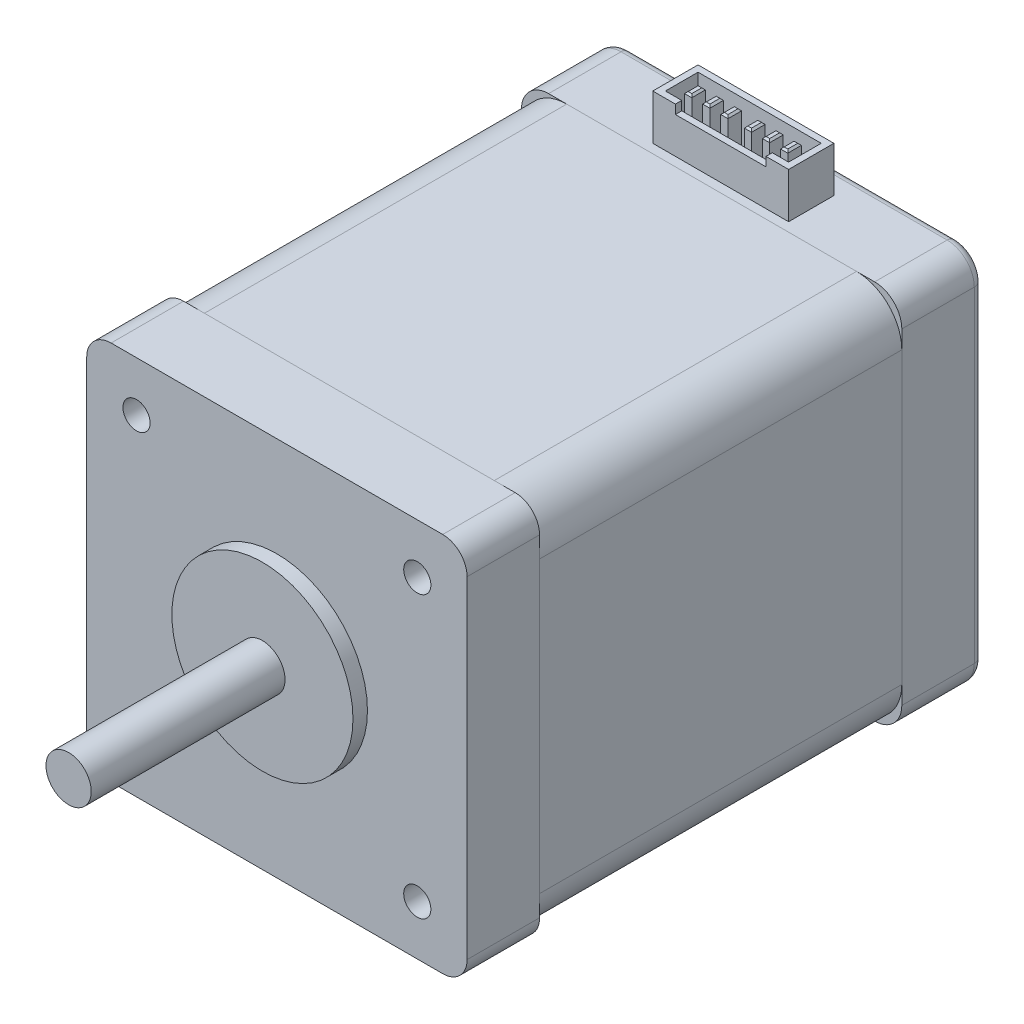
SolidWorks part; units mm, degrees
ref_plane "Front Plane" through (0, 0, 0) normal (0, 0, 1) x (1, 0, 0)
ref_plane "Top Plane" through (0, 0, 0) normal (0, 1, 0) x (1, 0, 0)
ref_plane "Right Plane" through (0, 0, 0) normal (1, 0, 0) x (0, 0, -1)
sketch "Sketch1" plane through (0, 0, 0) normal (0, 0, 1) x (1, 0, 0)
  line L0 (0, -25.0824) -> (0, 25.0824) construction
  line L1 (27.865, 0) -> (-27.865, 0) construction
  line L2 (-18.3073, -21) -> (18.3073, -21)
  line L3 (-21, -18.3073) -> (-21, 18.3073)
  line L4 (-18.3073, 21) -> (18.3073, 21)
  line L5 (21, -18.3073) -> (21, 18.3073)
  line L6 (-21, -21) -> (21, 21) construction
  line L7 (-21, 21) -> (21, -21) construction
  line L8 (-15.5, 15.5) -> (-15.5, -15.5) construction
  line L9 (-15.5, -15.5) -> (15.5, -15.5) construction
  line L10 (15.5, -15.5) -> (15.5, 15.5) construction
  line L11 (15.5, 15.5) -> (-15.5, 15.5) construction
  circle A0 centre (-15.5, 15.5) radius 1.5
  circle A1 centre (15.5, 15.5) radius 1.5
  circle A2 centre (15.5, -15.5) radius 1.5
  circle A3 centre (-15.5, -15.5) radius 1.5
  arc A4 (-21, -18.3073) -> (-18.3073, -21) centre (-18.3073, -18.3073) ccw
  arc A5 (-18.3073, 21) -> (-21, 18.3073) centre (-18.3073, 18.3073) ccw
  arc A6 (21, 18.3073) -> (18.3073, 21) centre (18.3073, 18.3073) ccw
  arc A7 (18.3073, -21) -> (21, -18.3073) centre (18.3073, -18.3073) ccw
  point P0 (0, 0)
  point P4 (0, 0)
  point P13 (0, 0)
  point P35 (0, 0)
  dimension "D3" = 3
  dimension "D1" = 42
  dimension "D2" = 42
  dimension "D4" = 31
  dimension "D5" = 4
extrude "Boss-Extrude1" add sketch "Sketch1" along normal blind 8
sketch "Sketch2" plane through (0, 0, 8) normal (0, 0, 1) x (1, 0, 0)
  circle A0 centre (0, 0) radius 2.5
  dimension "D1" = 5
extrude "Boss-Extrude2" add sketch "Sketch2" along normal blind 23
sketch "Sketch3" plane through (0, 0, 0) normal (0, 0, -1) x (-1, 0, 0)
  line L1 (-21, -21) -> (21, -21)
  line L2 (-21, -21) -> (-21, 21)
  line L3 (-21, 21) -> (21, 21)
  line L4 (21, -21) -> (21, 21)
  line L5 (-21, -21) -> (21, 21) construction
  line L6 (-21, 21) -> (21, -21) construction
  point P0 (0, 0)
  dimension "D1" = 42
  dimension "D2" = 42
extrude "Boss-Extrude3" add sketch "Sketch3" along normal blind 40 separate body
sketch "Sketch4" plane through (0, 0, -40) normal (0, 0, -1) x (-1, 0, 0)
  line L0 (21, -21) -> (21, 21) construction
  line L1 (-21, -21) -> (21, -21) construction
  line L2 (-21, 21) -> (-21, -21) construction
  line L3 (21, 21) -> (-21, 21) construction
  line L4 (21, -21) -> (21, 21)
  line L5 (-21, -21) -> (21, -21)
  line L6 (-21, 21) -> (-21, -21)
  line L7 (21, 21) -> (-21, 21)
extrude "Boss-Extrude4" add sketch "Sketch4" along normal blind 9 separate body
fillet "Fillet1" radius 3 4 edges at (-21, -21, -44.5) (21, -21, -44.5) (21, 21, -44.5) (-21, 21, -44.5)
fillet "Fillet3" radius 5 4 edges at (-21, 21, -20) (-21, -21, -20) (21, -21, -20) (21, 21, -20)
sketch "Sketch5" plane through (0, 0, -49) normal (0, 0, -1) x (-1, 0, 0)
  circle A0 centre (-15.5, 15.5) radius 1.5 construction
  circle A1 centre (-15.5, 15.5) radius 1.5
  circle A2 centre (-15.5, -15.5) radius 1.5 construction
  circle A3 centre (-15.5, -15.5) radius 1.5
  circle A4 centre (15.5, 15.5) radius 1.5 construction
  circle A5 centre (15.5, 15.5) radius 1.5
  circle A6 centre (15.5, -15.5) radius 1.5 construction
  circle A7 centre (15.5, -15.5) radius 1.5
extrude "Cut-Extrude1" cut sketch "Sketch5" against normal through all
sketch "Sketch6" plane through (0, 0, 8) normal (0, 0, 1) x (1, 0, 0)
  circle A0 centre (0, 0) radius 10
  circle A1 centre (0, 0) radius 2.5 construction
  circle A2 centre (0, 0) radius 2.5
  dimension "D1" = 20
extrude "Boss-Extrude5" add sketch "Sketch6" along normal blind 1.6
sketch "Sketch7" plane through (0, 21, 0) normal (0, 1, 0) x (1, 0, 0)
  line L0 (0, 0) -> (0, 52.3283) construction
  line L1 (0, 46) -> (-7.5, 46)
  line L2 (-7.5, 46) -> (-7.5, 41)
  line L3 (-7.5, 41) -> (7.5, 41)
  line L4 (7.5, 41) -> (7.5, 46)
  line L5 (7.5, 46) -> (0, 46)
  line L6 (-18, 49) -> (18, 49) construction
  line L7 (0, 45.3) -> (-6.8, 45.3)
  line L8 (-6.8, 45.3) -> (-6.8, 41.7)
  line L9 (-6.8, 41.7) -> (0, 41.7)
  line L10 (0, 41.7) -> (6.8, 41.7)
  line L11 (6.8, 41.7) -> (6.8, 45.3)
  line L12 (6.8, 45.3) -> (0, 45.3)
  line L13 (-6.2801, 43.457) -> (-4.7801, 43.457) construction
  line L15 (-5.7, 42.707) -> (-4.9, 42.707)
  line L16 (-5.7, 42.707) -> (-5.7, 44.207)
  line L17 (-5.7, 44.207) -> (-4.9, 44.207)
  line L18 (-4.9, 42.707) -> (-4.9, 44.207)
  line L19 (-5.7, 42.707) -> (-4.9, 44.207) construction
  line L20 (-5.7, 44.207) -> (-4.9, 42.707) construction
  line L21 (-3.7, 42.707) -> (-2.9, 42.707)
  line L22 (-3.7, 42.707) -> (-3.7, 44.207)
  line L23 (-3.7, 44.207) -> (-2.9, 44.207)
  line L24 (-2.9, 42.707) -> (-2.9, 44.207)
  line L25 (-3.7, 42.707) -> (-2.9, 44.207) construction
  line L26 (-3.7, 44.207) -> (-2.9, 42.707) construction
  line L27 (-0.9, 42.707) -> (-1.7, 42.707)
  line L28 (-0.9, 42.707) -> (-0.9, 44.207)
  line L29 (-0.9, 44.207) -> (-1.7, 44.207)
  line L30 (-1.7, 42.707) -> (-1.7, 44.207)
  line L31 (-0.9, 42.707) -> (-1.7, 44.207) construction
  line L32 (-0.9, 44.207) -> (-1.7, 42.707) construction
  line L33 (0.9, 42.707) -> (1.7, 42.707)
  line L34 (0.9, 42.707) -> (0.9, 44.207)
  line L35 (0.9, 44.207) -> (1.7, 44.207)
  line L36 (1.7, 42.707) -> (1.7, 44.207)
  line L37 (0.9, 42.707) -> (1.7, 44.207) construction
  line L38 (0.9, 44.207) -> (1.7, 42.707) construction
  line L39 (2.9, 42.707) -> (3.7, 42.707)
  line L40 (2.9, 42.707) -> (2.9, 44.207)
  line L41 (2.9, 44.207) -> (3.7, 44.207)
  line L42 (3.7, 42.707) -> (3.7, 44.207)
  line L43 (2.9, 42.707) -> (3.7, 44.207) construction
  line L44 (2.9, 44.207) -> (3.7, 42.707) construction
  line L45 (4.9, 42.707) -> (5.7, 42.707)
  line L46 (4.9, 42.707) -> (4.9, 44.207)
  line L47 (4.9, 44.207) -> (5.7, 44.207)
  line L48 (5.7, 42.707) -> (5.7, 44.207)
  line L49 (4.9, 42.707) -> (5.7, 44.207) construction
  line L50 (4.9, 44.207) -> (5.7, 42.707) construction
  point P18 (-5.3, 43.457)
  point P23 (-3.3, 43.457)
  point P28 (-1.3, 43.457)
  point P33 (1.3, 43.457)
  point P38 (3.3, 43.457)
  point P43 (5.3, 43.457)
  dimension "D1" = 15
  dimension "D2" = 3
  dimension "D3" = 5
  dimension "D4" = 0.7
  dimension "D5" = 0.7
  dimension "D6" = 0.7
  dimension "D7" = 1.843
  dimension "D8" = 1.5
  dimension "D9" = 0.8
  dimension "D10" = 0.8
  dimension "D11" = 1.5
  dimension "D12" = 0.8
  dimension "D13" = 1.5
  dimension "D14" = 0.8
  dimension "D15" = 0.8
  dimension "D16" = 0.8
  dimension "D17" = 1.5
  dimension "D18" = 1.5
  dimension "D19" = 1.5
  dimension "D20" = 1.5
  dimension "D21" = 2
  dimension "D22" = 2
  dimension "D23" = 2
  dimension "D24" = 2
  dimension "D25" = 1.5
extrude "Boss-Extrude6" add sketch "Sketch7" along normal blind 5 contours L4 L5 L1 L2 L3 L12 L11 L10 L9 L8 L7 | L15 L18 L17 L16 | L21 L24 L23 L22 | L30 L27 L28 L29 | L33 L36 L35 L34 | L39 L42 L41 L40 | L45 L48 L47 L46
chamfer "Chamfer1" distance 0.2 angle 45 24 edges at (4.9, 26, -43.457) (5.3, 26, -44.207) (5.7, 26, -43.457) (5.3, 26, -42.707) (2.9, 26, -43.457) (3.3, 26, -44.207) (3.7, 26, -43.457) (3.3, 26, -42.707) (0.9, 26, -43.457) (1.3, 26, -44.207) (1.7, 26, -43.457) (1.3, 26, -42.707) (-1.3, 26, -44.207) (-0.9, 26, -43.457) (-1.3, 26, -42.707) (-1.7, 26, -43.457) (-3.7, 26, -43.457) (-3.3, 26, -44.207) (-2.9, 26, -43.457) (-3.3, 26, -42.707) (-5.7, 26, -43.457) (-5.3, 26, -44.207) (-4.9, 26, -43.457) (-5.3, 26, -42.707)
sketch "Sketch8" plane through (0, 0, -41) normal (0, 0, 1) x (1, 0, 0)
  line L0 (0, 0) -> (0, 27.601) construction
  line L1 (5, 26) -> (-5, 26)
  line L2 (-7.5, 26) -> (7.5, 26) construction
  line L3 (-5, 26) -> (-5, 25)
  line L4 (-5, 25) -> (5, 25)
  line L5 (5, 26) -> (5, 25)
  point P10 (0, 26)
  point P11 (0, 25)
  dimension "D1" = 5
  dimension "D2" = 1
extrude "Cut-Extrude2" cut sketch "Sketch8" against normal up to next (0.7 mm away)
fillet "Fillet5" radius 1 8 edges at (-20.1213, 20.1213, -49) (-21, 0, -49) (-20.1213, -20.1213, -49) (0, -21, -49) (20.1213, -20.1213, -49) (21, 0, -49) (20.1213, 20.1213, -49) (0, 21, -49)
sketch "Sketch9" plane through (0, 0, 31) normal (0, 0, 1) x (1, 0, 0)
  line L0 (0, 0) -> (0, 6.8204) construction
